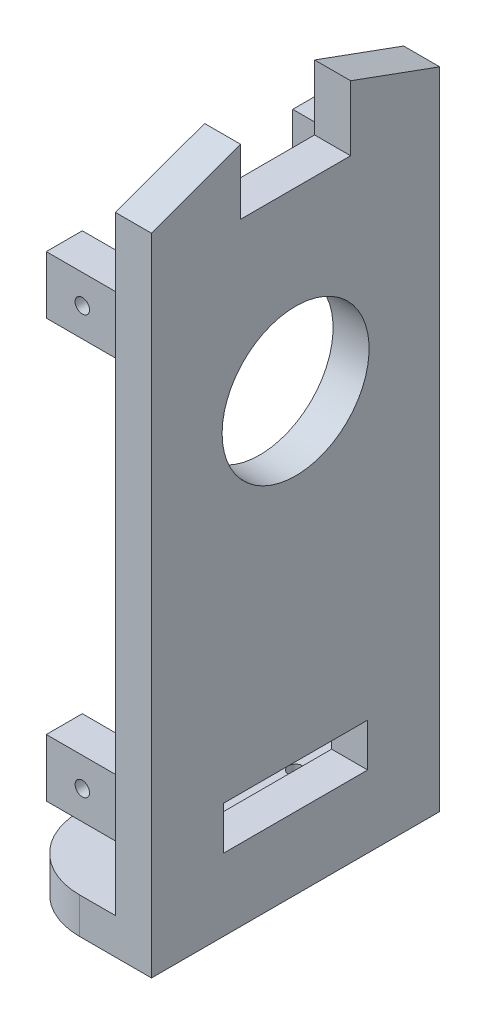
SolidWorks part; units mm, degrees
ref_plane "Front Plane" through (0, 0, 0) normal (0, 0, 1) x (1, 0, 0)
ref_plane "Top Plane" through (0, 0, 0) normal (0, 1, 0) x (1, 0, 0)
ref_plane "Right Plane" through (0, 0, 0) normal (1, 0, 0) x (0, 0, -1)
sketch "Sketch1" plane through (0, 0, 0) normal (0, 1, 0) x (1, 0, 0)
  line L0 (5.3196, -11.3329) -> (15.3196, -11.3329)
  line L1 (15.3196, -11.3329) -> (15.3196, 28.6671)
  line L2 (15.3196, 28.6671) -> (5.3196, 28.6671)
  line L3 (-4.6804, 18.6671) -> (-4.6804, -1.3329)
  arc A0 (5.3196, 28.6671) -> (-4.6804, 18.6671) centre (5.3196, 18.6671) ccw
  arc A1 (-4.6804, -1.3329) -> (5.3196, -11.3329) centre (5.3196, -1.3329) ccw
  circle A2 centre (5.3196, 18.6671) radius 1
  circle A3 centre (5.3196, -1.3329) radius 1
extrude "Boss-Extrude1" add sketch "Sketch1" along normal blind 5
sketch "Sketch2" plane through (0, 5, 0) normal (0, 1, 0) x (1, 0, 0)
  line L0 (15.3196, 28.6671) -> (15.3196, -11.3329)
  line L1 (15.3196, 28.6671) -> (10.3196, 28.6671)
  line L2 (15.3196, -11.3329) -> (10.3196, -11.3329)
  line L3 (10.3196, 28.6671) -> (10.3196, -11.3329)
  dimension "D1" = 5
extrude "Boss-Extrude2" add sketch "Sketch2" along normal blind 80
sketch "Sketch3" plane through (10.3196, 0, 0) normal (-1, 0, 0) x (0, 0, 1)
  line L0 (-8.6671, 85) -> (-8.6671, 5) construction
  line L1 (-28.6671, 85) -> (11.3329, 85) construction
  line L2 (-18.6671, 5) -> (1.3329, 5) construction
  line L4 (1.3329, 36.402) -> (1.3329, 60.5442)
  line L5 (-18.0671, 35.802) -> (0.7329, 35.802)
  line L7 (-18.6671, 60.5442) -> (-18.6671, 36.402)
  line L10 (-18.6671, 69.9442) -> (-18.6671, 60.5442)
  line L11 (-8.6671, 70.5442) -> (-12.0788, 70.5442)
  line L12 (-12.0788, 70.5442) -> (-18.0671, 70.5442)
  line L14 (-5.2553, 70.5442) -> (-8.6671, 70.5442)
  line L16 (0.7329, 70.5442) -> (-5.2553, 70.5442)
  line L17 (1.3329, 60.5442) -> (1.3329, 69.9442)
  line L19 (1.7329, 36.402) -> (1.7329, 60.5442)
  line L20 (1.7329, 60.5442) -> (1.7329, 69.9442)
  line L21 (0.7329, 70.9442) -> (-5.2553, 70.9442)
  line L22 (-5.2553, 70.9442) -> (-8.6671, 70.9442)
  line L23 (-8.6671, 70.9442) -> (-12.0788, 70.9442)
  line L24 (-12.0788, 70.9442) -> (-18.0671, 70.9442)
  line L25 (-19.0671, 69.9442) -> (-19.0671, 60.5442)
  line L26 (-19.0671, 60.5442) -> (-19.0671, 36.402)
  line L27 (-18.0671, 35.402) -> (0.7329, 35.402)
  arc A1 (0.7329, 35.802) -> (1.3329, 36.402) centre (0.7329, 36.402) ccw
  arc A2 (-18.6671, 36.402) -> (-18.0671, 35.802) centre (-18.0671, 36.402) ccw
  arc A5 (-18.0671, 70.5442) -> (-18.6671, 69.9442) centre (-18.0671, 69.9442) ccw
  arc A8 (1.3329, 69.9442) -> (0.7329, 70.5442) centre (0.7329, 69.9442) ccw
  arc A10 (-15.1231, 76.5942) -> (-11.2111, 76.5942) centre (-13.1671, 75.5442) ccw
  arc A11 (-11.2111, 24.1942) -> (-15.1231, 24.1942) centre (-13.1671, 25.2442) ccw
  arc A12 (-2.2111, 24.1942) -> (-6.1231, 24.1942) centre (-4.1671, 25.2442) ccw
  arc A13 (-6.1231, 76.5942) -> (-2.2111, 76.5942) centre (-4.1671, 75.5442) ccw
  arc A14 (1.7329, 69.9442) -> (0.7329, 70.9442) centre (0.7329, 69.9442) ccw
  arc A15 (-18.0671, 70.9442) -> (-19.0671, 69.9442) centre (-18.0671, 69.9442) ccw
  arc A16 (-19.0671, 36.402) -> (-18.0671, 35.402) centre (-18.0671, 36.402) ccw
  arc A17 (0.7329, 35.402) -> (1.7329, 36.402) centre (0.7329, 36.402) ccw
  circle A18 centre (-13.1671, 25.2442) radius 2.22
  circle A19 centre (-4.1671, 25.2442) radius 2.22
  circle A20 centre (-13.1671, 75.5442) radius 2.22
  circle A21 centre (-4.1671, 75.5442) radius 2.22
  dimension "D1" = 0.4
extrude "Cut-Extrude3" cut sketch "Sketch3" against normal blind 80 contours A12 A19 | A11 A18 | L0 L11 L12 A5 L10 L7 A2 L5 | L14 L0 L5 A1 L4 L17 A8 L16 | L0 L23 L24 A15 L25 L26 A16 L27 L5 A2 L7 L10 A5 L12 L11 | L22 L0 L14 L16 A8 L17 L4 A1 L5 L27 A17 L19 L20 A14 L21 | A13 A21 | A10 A20
sketch "Sketch5" plane through (15.3196, 0, 0) normal (1, 0, 0) x (0, 0, -1)
  circle A0 centre (4.1671, 25.2442) radius 2.22 construction
  circle A1 centre (13.1671, 25.2442) radius 2.22 construction
  circle A2 centre (4.1671, 75.5442) radius 2.22 construction
  circle A3 centre (13.1671, 75.5442) radius 2.22 construction
  circle A4 centre (4.1671, 25.2442) radius 2.22
  circle A5 centre (13.1671, 25.2442) radius 2.22
  circle A6 centre (4.1671, 75.5442) radius 2.22
  circle A7 centre (13.1671, 75.5442) radius 2.22
sketch "Sketch8" plane through (10.3196, 0, 0) normal (-1, 0, 0) x (0, 0, 1)
  line L0 (-28.6671, 85) -> (-28.6671, 89.5078)
  line L1 (-28.6671, 85) -> (11.3329, 85)
  line L2 (11.3329, 89.5078) -> (11.3329, 85)
  line L3 (-28.6671, 85) -> (11.3329, 85) construction
  line L4 (-16.3005, 85) -> (-1.0337, 85)
  line L5 (-16.3005, 85) -> (-16.3005, 94.0156)
  line L7 (-1.0337, 85) -> (-1.0337, 94.0156)
  line L10 (-28.6671, 89.5078) -> (-16.3005, 94.0156)
  line L11 (-1.0337, 94.0156) -> (11.3329, 89.5078)
  point P3 (-8.6671, 89.5078)
  line M14 (11.3329, 85) -> (-28.6671, 85)
extrude "Boss-Extrude5" add sketch "Sketch8" against normal through all contours L10 L0 L5 M14 | L11 L7 L2 M14
sketch "Sketch9" plane through (10.3196, 0, 0) normal (-1, 0, 0) x (0, 0, 1)
  line L0 (-18.6671, 5) -> (-18.6671, 10)
  line L1 (-18.6671, 10) -> (1.3329, 10)
  line L2 (1.3329, 10) -> (1.3329, 5)
  line L3 (-18.6671, 16) -> (-18.6671, 10)
  line L4 (-18.6671, 0) -> (1.3329, 0)
  line L5 (1.3329, 0) -> (1.3329, 5)
  line L6 (1.3329, 5) -> (-18.6671, 5)
  line L7 (-18.6671, 5) -> (-18.6671, 0)
  line L8 (-18.6671, 0) -> (1.3329, 0)
  line L9 (1.3329, 0) -> (1.3329, 5)
  line L10 (1.3329, 5) -> (-18.6671, 5)
  line L11 (-18.6671, 5) -> (-18.6671, 0)
  line L12 (-18.6671, 16) -> (1.3329, 16)
  line L13 (-18.6671, 10) -> (1.3329, 10)
  line L14 (1.3329, 16) -> (1.3329, 10)
  dimension "D2" = 5
  dimension "D3" = 6
  dimension "D1" = 0
extrude "Cut-Extrude7" cut sketch "Sketch9" against normal blind 10 contours L14 L12 L3 L1
sketch "Sketch10" plane through (10.3196, 0, 0) normal (-1, 0, 0) x (0, 0, 1)
  line L0 (-28.2671, 5.4) -> (10.9329, 5.4)
  line L1 (10.9329, 5.4) -> (10.9329, 89.2279)
  line L2 (10.9329, 89.2279) -> (-0.6337, 93.444)
  line L3 (-0.6337, 93.444) -> (-0.6337, 84.6)
  line L4 (-0.6337, 84.6) -> (-16.7005, 84.6)
  line L5 (-16.7005, 84.6) -> (-16.7005, 93.444)
  line L6 (-16.7005, 93.444) -> (-28.2671, 89.2279)
  line L7 (-28.2671, 89.2279) -> (-28.2671, 5.4)
  line L8 (-28.6671, 5) -> (11.3329, 5)
  line L9 (11.3329, 5) -> (11.3329, 89.5078)
  line L10 (11.3329, 89.5078) -> (-1.0337, 94.0156)
  line L11 (-1.0337, 94.0156) -> (-1.0337, 85)
  line L12 (-1.0337, 85) -> (-16.3005, 85)
  line L13 (-16.3005, 85) -> (-16.3005, 94.0156)
  line L14 (-16.3005, 94.0156) -> (-28.6671, 89.5078)
  line L15 (-28.6671, 89.5078) -> (-28.6671, 5)
  line L16 (-28.6671, 5) -> (11.3329, 5)
  line L17 (11.3329, 5) -> (11.3329, 89.5078)
  line L18 (11.3329, 89.5078) -> (-1.0337, 94.0156)
  line L19 (-1.0337, 94.0156) -> (-1.0337, 85)
  line L20 (-1.0337, 85) -> (-16.3005, 85)
  line L21 (-16.3005, 85) -> (-16.3005, 94.0156)
  line L22 (-16.3005, 94.0156) -> (-28.6671, 89.5078)
  line L23 (-28.6671, 89.5078) -> (-28.6671, 5)
  line L24 (-28.2671, 5.4) -> (-23.2671, 5.4)
  line L25 (-28.2671, 5.4) -> (-28.2671, 13.5669)
  line L26 (-23.2671, 5.4) -> (-23.2671, 13.5669)
  line L27 (-28.2671, 13.5669) -> (-23.2671, 13.5669)
  line L28 (-28.2671, 13.5669) -> (-23.2671, 13.5669)
  line L29 (-28.2671, 13.5669) -> (-28.2671, 21.5669)
  line L30 (-23.2671, 13.5669) -> (-23.2671, 21.5669)
  line L31 (-28.2671, 21.5669) -> (-23.2671, 21.5669)
  line L32 (-28.2671, 84.6) -> (-23.2671, 84.6)
  line L33 (-28.2671, 84.6) -> (-28.2671, 79.6)
  line L34 (-23.2671, 84.6) -> (-23.2671, 79.6)
  line L35 (-28.2671, 79.6) -> (-23.2671, 79.6)
  line L36 (-28.2671, 79.6) -> (-23.2671, 79.6)
  line L37 (-28.2671, 79.6) -> (-28.2671, 71.6)
  line L38 (-23.2671, 79.6) -> (-23.2671, 71.6)
  line L39 (-28.2671, 71.6) -> (-23.2671, 71.6)
  line L40 (-8.6671, 84.6) -> (-8.6671, 5.4) construction
  line L41 (10.9329, 71.6) -> (5.9329, 71.6)
  line L42 (5.9329, 79.6) -> (5.9329, 71.6)
  line L43 (10.9329, 79.6) -> (10.9329, 71.6)
  line L44 (10.9329, 79.6) -> (5.9329, 79.6)
  line L45 (10.9329, 79.6) -> (5.9329, 79.6)
  line L46 (5.9329, 84.6) -> (5.9329, 79.6)
  line L47 (10.9329, 84.6) -> (10.9329, 79.6)
  line L48 (10.9329, 84.6) -> (5.9329, 84.6)
  line L49 (10.9329, 21.5669) -> (5.9329, 21.5669)
  line L50 (5.9329, 13.5669) -> (5.9329, 21.5669)
  line L51 (10.9329, 13.5669) -> (10.9329, 21.5669)
  line L52 (10.9329, 13.5669) -> (5.9329, 13.5669)
  line L53 (10.9329, 13.5669) -> (5.9329, 13.5669)
  line L54 (5.9329, 5.4) -> (5.9329, 13.5669)
  line L55 (10.9329, 5.4) -> (10.9329, 13.5669)
  line L56 (10.9329, 5.4) -> (5.9329, 5.4)
  line L57 (11.3329, 89.5078) -> (11.3329, 5)
  line L58 (-1.0337, 94.0156) -> (11.3329, 89.5078)
  line L59 (10.9329, 89.2279) -> (10.9329, 5.4)
  line L60 (-0.6337, 93.444) -> (10.9329, 89.2279)
  line L61 (-0.6337, 84.6) -> (-0.6337, 93.444)
  dimension "D3" = 5
  dimension "D4" = 8
  dimension "D5" = 5
  dimension "D6" = 8
  dimension "D1" = 0
  dimension "D2" = 0.4
extrude "Boss-Extrude6" add sketch "Sketch10" along normal blind 10 contours L31 L7 L27 L30 | L52 L1 L49 L50 | L1 L44 L42 L41 | L7 L39 L38 L35
sketch "Sketch11" plane through (0, 0, 10.9329) normal (0, 0, 1) x (1, 0, 0)
  line L0 (0.3196, 79.6) -> (10.3196, 71.6) construction
  line L1 (10.3196, 71.6) -> (10.3196, 21.5669) construction
  line L2 (10.3196, 21.5669) -> (0.3196, 13.5669) construction
  circle A0 centre (5.3196, 17.5669) radius 1
  circle A1 centre (5.3196, 75.6) radius 1
  dimension "D1" = 2
  dimension "D2" = 2
extrude "Cut-Extrude9" cut sketch "Sketch11" against normal blind 8
sketch "Sketch12" plane through (0, 0, -28.2671) normal (0, 0, -1) x (-1, 0, 0)
  circle A0 centre (-5.3196, 75.6) radius 1 construction
  circle A1 centre (-5.3196, 17.5669) radius 1 construction
  circle A2 centre (-5.3196, 75.6) radius 1
  circle A3 centre (-5.3196, 17.5669) radius 1
extrude "Cut-Extrude10" cut sketch "Sketch12" against normal blind 8
extrude "Boss-Extrude7" add sketch "Sketch5" against normal up to surface (5 mm away) up to face at (10.3196, 75.6, 8.4329)
sketch "Sketch14" plane through (10.3196, 0, 0) normal (-1, 0, 0) x (0, 0, 1)
  line L0 (-8.6671, 85) -> (-8.6671, 60.54) construction
  line L1 (-16.3005, 85) -> (-1.0337, 85) construction
  line L2 (0.7329, 70.9442) -> (-18.0671, 70.9442) construction
  line L3 (-19.0671, 69.9442) -> (-19.0671, 36.402) construction
  line L4 (-18.0671, 35.402) -> (0.7329, 35.402) construction
  line L5 (1.7329, 36.402) -> (1.7329, 69.9442) construction
  line L6 (0.7329, 70.9442) -> (-18.0671, 70.9442)
  line L7 (-19.0671, 69.9442) -> (-19.0671, 36.402)
  line L8 (-18.0671, 35.402) -> (0.7329, 35.402)
  line L9 (1.7329, 36.402) -> (1.7329, 69.9442)
  circle A0 centre (-8.6671, 60.54) radius 10.2
  arc A1 (1.7329, 69.9442) -> (0.7329, 70.9442) centre (0.7329, 69.9442) ccw construction
  arc A2 (-18.0671, 70.9442) -> (-19.0671, 69.9442) centre (-18.0671, 69.9442) ccw construction
  arc A3 (-19.0671, 36.402) -> (-18.0671, 35.402) centre (-18.0671, 36.402) ccw construction
  arc A4 (0.7329, 35.402) -> (1.7329, 36.402) centre (0.7329, 36.402) ccw construction
  arc A5 (1.7329, 69.9442) -> (0.7329, 70.9442) centre (0.7329, 69.9442) ccw
  arc A6 (-18.0671, 70.9442) -> (-19.0671, 69.9442) centre (-18.0671, 69.9442) ccw
  arc A7 (-19.0671, 36.402) -> (-18.0671, 35.402) centre (-18.0671, 36.402) ccw
  arc A8 (0.7329, 35.402) -> (1.7329, 36.402) centre (0.7329, 36.402) ccw
  dimension "D2" = 20.4
  dimension "D1" = 24.46
extrude "Boss-Extrude8" add sketch "Sketch14" against normal up to surface (5 mm away) up to face at (15.3196, 67.1308, -8.6671)
